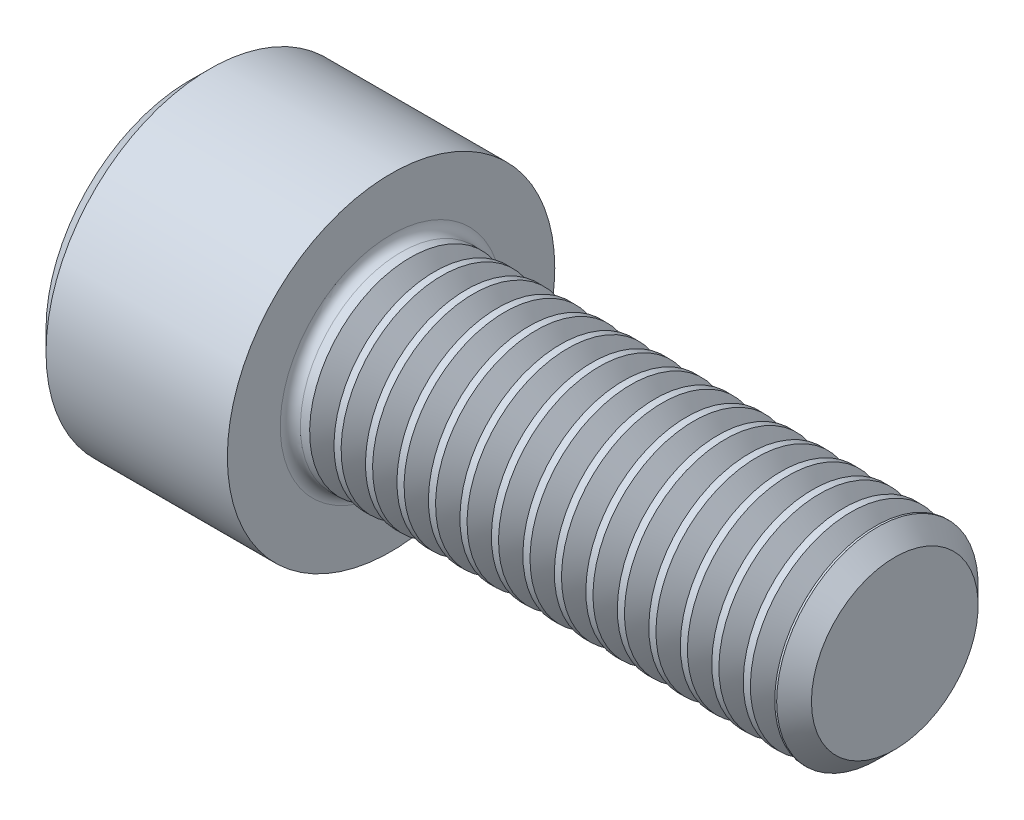
SolidWorks part; units mm, degrees
revolve "Base-Revolve" add sketch "BodySke"
sketch "BodySke" plane through (0, 0, 0) normal (0, 0, 1) x (1, 0, 0)
  line L0 (0, 0) -> (0, 5.7)
  line L1 (0.8, 6.5) -> (8, 6.5)
  line L2 (8, 6.5) -> (8, 4)
  line L3 (8, 4) -> (27.3095, 4)
  line L4 (28, 3.3095) -> (28, 0)
  line L5 (28, 0) -> (0, 0)
  line L6 (-31.75, 0) -> (127, 0) construction
  line L7 (0, 5.7) -> (0.8, 6.5)
  line L8 (28, 3.3095) -> (27.3095, 4)
  line L9 (0, -5.7) -> (0.8, -6.5) construction
  line L10 (28, -3.3095) -> (27.3095, -4) construction
  line L11 (9.25, 9.525) -> (9.25, 3.175) construction
  line L12 (8, 9.525) -> (8, 3.175) construction
  line L13 (-22, 9.525) -> (-22, 3.175) construction
  dimension "Diameter" = 8
  dimension "Head_ht" = 8
  dimension "Length" = 20
  dimension "Body_ch_ang" = 45
  dimension "Head_dia" = 13
  dimension "Head_ch_ang" = 45
  dimension "Minor_dia" = 6.619
  dimension "Advance" = 1.25
  dimension "Thread_nom" = 20
  dimension "Thread_length" = 50
  dimension "Head_ch_ht" = 0.8
cosmetic thread "ThreadCosmetic" [suppressed]
fillet "Fillet1" radius 0.4 1 edges at (8, 0, 4)
ref_plane "Plane1" through (0, 0, 0) normal (0, 0, 1) x (1, 0, 0)
ref_plane "Plane2" through (0, 0, 0) normal (0, 1, 0) x (1, 0, 0)
ref_plane "Plane3" through (0, 0, 0) normal (1, 0, 0) x (0, 0, -1)
sketch "Sketch2" plane through (0, 0, 0) normal (0, 0, 1) x (1, 0, 0)
  line L0 (0, 3.0475) -> (4, 3.0475)
  line L1 (4, 3.0475) -> (5.7595, 0)
  line L2 (-31.75, 0) -> (127, 0) construction
  line L3 (5.7595, 0) -> (0, 0)
  line L4 (0, 0) -> (0, 3.0475)
  line L5 (0, 5.7) -> (0, -5.7) construction
  line L6 (0, 0) -> (47.625, 0) construction
  line L7 (8, -6.5) -> (8, 6.5) construction
  dimension "D1" = 3.0475
  dimension "D2" = 60
revolve "Hex-PreBroach" cut sketch "Sketch2" angle 360 about L6
sketch "Sketch3" plane through (0, 0, 0) normal (-1, 0, 0) x (0, 0.5, 0.866)
  line L0 (1.7595, 3.0475) -> (-1.7595, 3.0475)
  line L1 (-1.7595, 3.0475) -> (-3.5189, 0)
  line L2 (1.7595, 3.0475) -> (3.5189, 0)
  line L3 (1.7595, -3.0475) -> (3.5189, 0)
  line L4 (1.7595, -3.0475) -> (-1.7595, -3.0475)
  line L5 (-1.7595, -3.0475) -> (-3.5189, 0)
  dimension "D1" = 3.0475
  dimension "D2" = 3.0475
  dimension "Hex_size" = 6.095
extrude "Hex" cut sketch "Sketch3" against normal blind 4
sketch "Sketch4" plane through (0, 0, 0) normal (-1, 0, 0) x (0, 0, 1)
  line L0 (0, 0) -> (3.7846, 0)
  line L1 (0, 0) -> (6.1484, 3.5498) construction
  line L2 (0, 0) -> (1.8923, 3.2776)
  line L3 (3.1235, 0.8061) -> (3.6229, 1.0945)
  line L4 (2.2599, 2.3019) -> (2.7593, 2.5903)
  arc A0 (3.1235, 0.8061) -> (2.2599, 2.3019) centre (0, 0) ccw
  arc A1 (3.7846, 0) -> (3.6229, 1.0945) centre (0, 0) ccw
  arc A2 (1.8923, 3.2776) -> (2.7593, 2.5903) centre (0, 0) cw
  dimension "D1" = 30
  dimension "D2" = 60
  dimension "Spline_p_dim" = 1.7272
  dimension "D3" = 0.8636
extrude "Spline" [suppressed] cut sketch "Sketch4" against normal blind 4
pattern_circular "CirPattern1" [suppressed] count 6 every 60
sketch "Sketch5" plane through (0, 0, 0) normal (0, 0, 1) x (1, 0, 0)
  line L0 (-31.75, 0) -> (127, 0) construction
  line L2 (0, 5.7) -> (0, -5.7) construction
  circle A0 centre (2.7, 0) radius 0.675
  dimension "Drilled_hole_dia" = 1.35
  dimension "Drilled_hole_loc" = 2.7
extrude "Hole" [suppressed] cut sketch "Sketch5" against normal through all and the other way through all
pattern_circular "Drilled-4" [suppressed] count 2 every 60
pattern_circular "Drilled-6" [suppressed] count 3 every 60
sketch "ThdSchSke" plane through (0, 0, 0) normal (0, 0, 1) x (1, 0, 0)
  line L0 (9.25, -3.3095) -> (8.7665, -4)
  line L1 (9.25, -3.3095) -> (9.7335, -4)
  line L2 (9.7335, -4) -> (9.7335, -5)
  line L3 (-3.175, 0) -> (5.1513, 0) construction
  line L5 (9.7335, -5) -> (8.7665, -5)
  line L6 (8.7665, -5) -> (8.7665, -4)
  line L7 (0, 5.7) -> (0, -5.7) construction
  dimension "Thread_minor" = 6.619
  dimension "Diameter" = 8
  dimension "Start" = 9.25
revolve "ThreadSchematic" cut sketch "ThdSchSke" angle 360 about L3
pattern_linear "ThdSchPat" count 15 spacing 1.25 along (1, 0, 0) of "ThreadSchematic"
equation "\"D2@Sketch3\" = \"Hex_size@Sketch3\" / 2"
equation "\"D1@Sketch3\" = \"Hex_size@Sketch3\" / 2"
equation "\"D1@Sketch2\" = \"Hex_size@Sketch3\" / 2"
equation "\"D3@Sketch4\" = \"Spline_p_dim@Sketch4\" / 2"
equation "\"Thread_minor@ThreadCosmetic\"  =  \"Minor_dia@BodySke\""
equation "\"D2@CirPattern1\" = 360 / \"Num_teeth@CirPattern1\""
equation "\"Wall_thickness@Sketch2\" = \"Head_ht@BodySke\" - \"Key_eng@Hex\""
equation "\"Thread_length@ThreadCosmetic\" = ((sgn( (\"Length@BodySke\" - \"Advance@BodySke\" ) - \"Thread_nom@BodySke\" )-1)*( (\"Length@BodySke\" - \"Advance@BodySke\" ) - \"Thread_nom@BodySke\" ))/-2+ \"Thread_nom@BodySke\""
equation "\"Thread_minor@ThdSchSke\" = \"Minor_dia@BodySke\""
equation "\"Diameter@ThdSchSke\" = \"Diameter@BodySke\""
equation "\"Overcut@ThdSchSke\" = \"Diameter@BodySke\" * 1.25"
equation "\"Start@ThdSchSke\" = \"Head_ht@BodySke\" + \"Length@BodySke\" - \"Thread_length@ThreadCosmetic\"  '---Non-countersunk---"
equation "\"Num_threads@ThdSchPat\" = int( \"Thread_length@ThreadCosmetic\" / \"Advance@BodySke\" + 0.999 )  + 1"
equation "\"Advance@ThdSchPat\" = \"Thread_length@ThreadCosmetic\" /  (\"Num_threads@ThdSchPat\" - 1) 'relax it"
equation "\"Num_threads@ThdSchPat\" = \"Num_threads@ThdSchPat\" - sgn( \"Num_threads@ThdSchPat\" - 1) '---chamfered tips only---"
